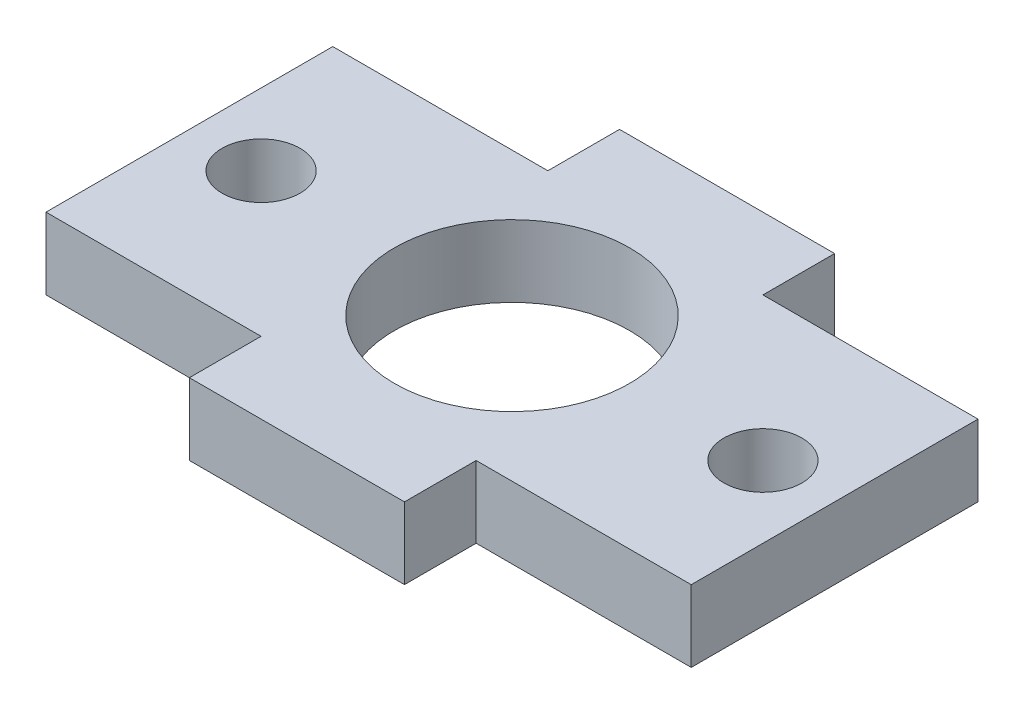
SolidWorks part; units mm, degrees
ref_plane "Front Plane" through (0, 0, 0) normal (0, 0, 1) x (1, 0, 0)
ref_plane "Top Plane" through (0, 0, 0) normal (0, 1, 0) x (1, 0, 0)
ref_plane "Right Plane" through (0, 0, 0) normal (1, 0, 0) x (0, 0, -1)
sketch "Sketch1" plane through (0, 0, 0) normal (0, 1, 0) x (1, 0, 0)
  line L0 (-22.225, 0) -> (22.225, 0) construction
  line L1 (-28.575, 12.7) -> (28.575, 12.7)
  line L2 (-28.575, 12.7) -> (-28.575, -12.7)
  line L3 (-28.575, -12.7) -> (28.575, -12.7)
  line L4 (28.575, 12.7) -> (28.575, -12.7)
  line L5 (-28.575, 12.7) -> (28.575, -12.7) construction
  line L6 (-28.575, -12.7) -> (28.575, 12.7) construction
  circle A0 centre (0, 0) radius 10.414
  circle A1 centre (-22.225, 0) radius 3.4544
  circle A2 centre (22.225, 0) radius 3.4544
  point P0 (0, 0)
  dimension "D1" = 20.828
  dimension "D4" = 6.9088
  dimension "D5" = 44.45
  dimension "D2" = 25.4
  dimension "D3" = 57.15
extrude "Boss-Extrude1" add sketch "Sketch1" along normal blind 6.35
sketch "Sketch2" plane through (0, 6.35, 0) normal (0, 1, 0) x (1, 0, 0)
  line L0 (28.575, 12.7) -> (-28.575, 12.7) construction
  line L1 (-9.525, 12.7) -> (9.525, 12.7)
  line L2 (-9.525, 12.7) -> (-9.525, 19.05)
  line L3 (-9.525, 19.05) -> (9.525, 19.05)
  line L4 (9.525, 12.7) -> (9.525, 19.05)
  point P6 (0, 19.05)
  dimension "D1" = 6.35
  dimension "D2" = 19.05
extrude "Boss-Extrude2" add sketch "Sketch2" against normal up to surface (6.35 mm away) up to face at (-22.225, 0, 3.4544)
mirror "Mirror1" about plane through (0, 0, 0) normal (0, 0, 1) of "Boss-Extrude2"
